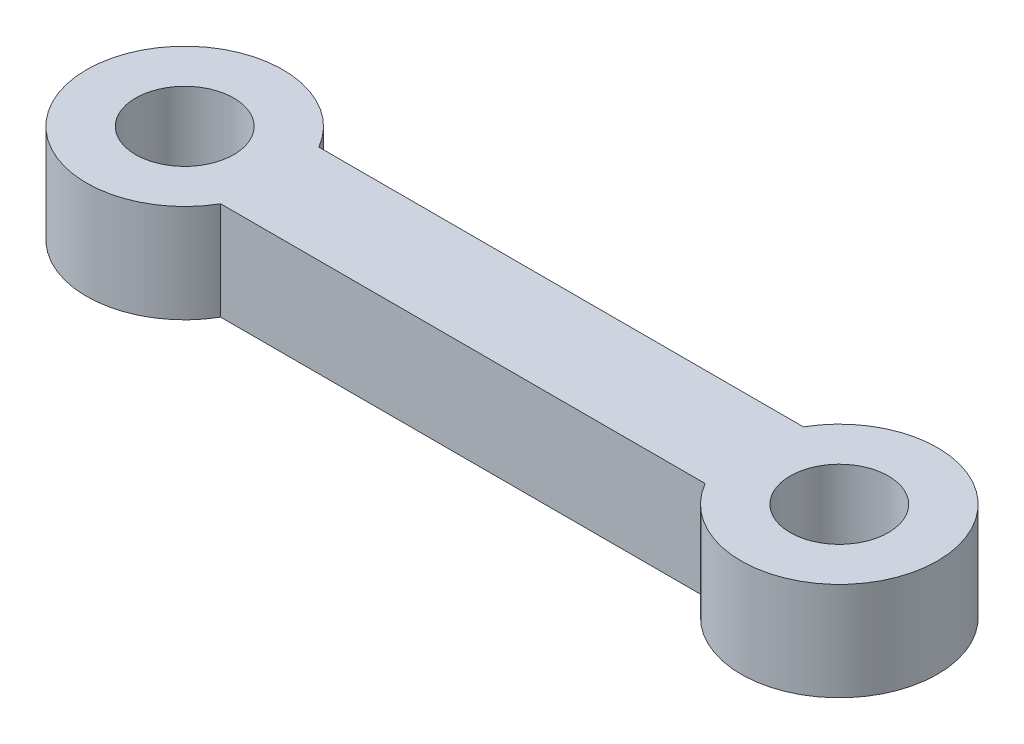
SolidWorks part; units mm, degrees
ref_plane "Front Plane" through (0, 0, 0) normal (0, 0, 1) x (1, 0, 0)
ref_plane "Top Plane" through (0, 0, 0) normal (0, 1, 0) x (1, 0, 0)
ref_plane "Right Plane" through (0, 0, 0) normal (1, 0, 0) x (0, 0, -1)
sketch "Sketch1" plane through (0, 0, 0) normal (0, 1, 0) x (1, 0, 0)
  line L1 (2.5981, 1.5) -> (17.4019, 1.5)
  line L4 (17.4019, -1.5) -> (2.5981, -1.5)
  circle A0 centre (0, 0) radius 1.5
  arc A1 (2.5981, 1.5) -> (2.5981, -1.5) centre (0, 0) ccw
  circle A6 centre (20, 0) radius 1.5
  arc A7 (17.4019, -1.5) -> (17.4019, 1.5) centre (20, 0) ccw
extrude "Boss-Extrude1" add sketch "Sketch1" along normal blind 3
